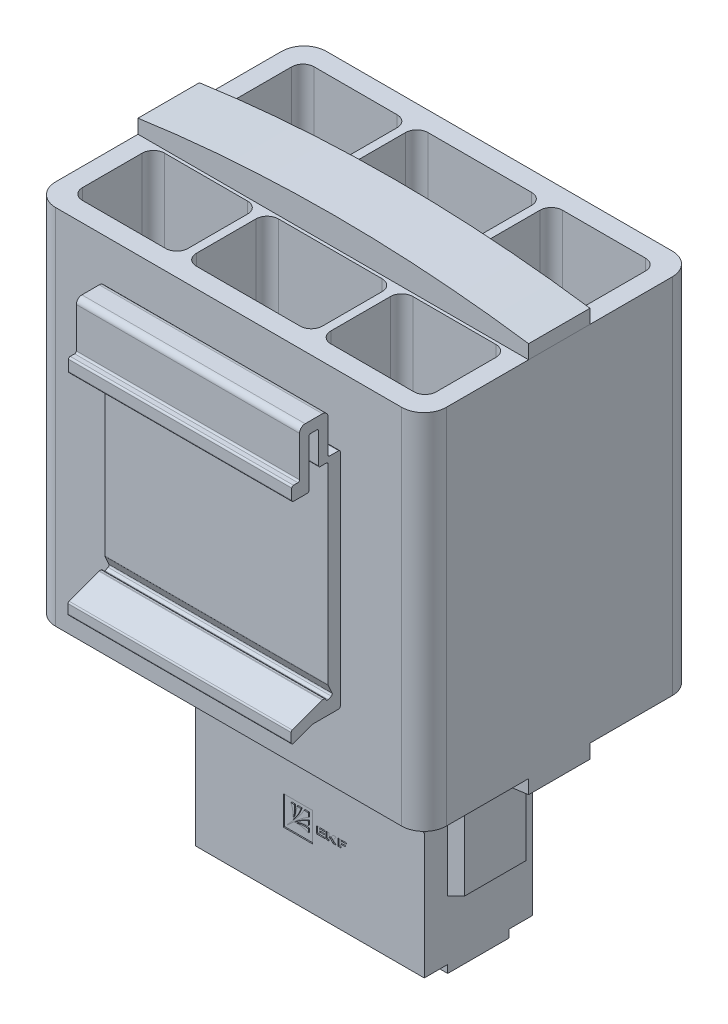
SolidWorks part; units mm, degrees
ref_plane "Спереди" through (0, 0, 0) normal (0, 0, 1) x (1, 0, 0)
ref_plane "Сверху" through (0, 0, 0) normal (0, 1, 0) x (1, 0, 0)
ref_plane "Справа" through (0, 0, 0) normal (1, 0, 0) x (0, 0, -1)
sketch "Эскиз1" plane through (0, 0, 0) normal (0, 0, 1) x (1, 0, 0)
  line L1 (-35, -32.5) -> (35, -32.5)
  line L2 (-35, -32.5) -> (-35, 32.5)
  line L3 (-35, 32.5) -> (35, 32.5)
  line L4 (35, -32.5) -> (35, 32.5)
  line L5 (-35, -32.5) -> (35, 32.5) construction
  line L6 (-35, 32.5) -> (35, -32.5) construction
  point P0 (0, 0)
  dimension "D1" = 70
  dimension "D2" = 65
extrude "Бобышка-Вытянуть1" add sketch "Эскиз1" along normal blind 48.5
sketch "Эскиз2" plane through (0, 32.5, 0) normal (0, 1, 0) x (1, 0, 0)
  line L0 (0, 0) -> (0, -10.85) construction
  line L1 (-11.3, -3.5) -> (11.3, -3.5)
  line L2 (-11.3, -3.5) -> (-11.3, -18.2)
  line L3 (-11.3, -18.2) -> (11.3, -18.2)
  line L4 (11.3, -3.5) -> (11.3, -18.2)
  line L5 (-11.3, -3.5) -> (11.3, -18.2) construction
  line L6 (-11.3, -18.2) -> (11.3, -3.5) construction
  line L7 (12.8, -3.5) -> (31.7, -3.5)
  line L8 (12.8, -3.5) -> (12.8, -18.2)
  line L9 (12.8, -18.2) -> (31.7, -18.2)
  line L10 (31.7, -3.5) -> (31.7, -18.2)
  line L11 (12.8, -3.5) -> (31.7, -18.2) construction
  line L12 (12.8, -18.2) -> (31.7, -3.5) construction
  line L13 (-31.7, -3.5) -> (-12.8, -3.5)
  line L14 (-31.7, -3.5) -> (-31.7, -18.2)
  line L15 (-31.7, -18.2) -> (-12.8, -18.2)
  line L16 (-12.8, -3.5) -> (-12.8, -18.2)
  line L17 (-31.7, -3.5) -> (-12.8, -18.2) construction
  line L18 (-31.7, -18.2) -> (-12.8, -3.5) construction
  line L19 (35, 0) -> (-35, 0) construction
  line L20 (-35, -24.25) -> (35, -24.25) construction
  line L21 (-35, -48.5) -> (-35, 0) construction
  line L22 (35, -48.5) -> (35, 0) construction
  line L23 (12.8, -30.3) -> (31.7, -30.3)
  line L24 (31.7, -45) -> (31.7, -30.3)
  line L25 (12.8, -45) -> (31.7, -45)
  line L26 (12.8, -45) -> (12.8, -30.3)
  line L27 (-11.3, -30.3) -> (11.3, -30.3)
  line L28 (11.3, -45) -> (11.3, -30.3)
  line L29 (-11.3, -45) -> (11.3, -45)
  line L30 (-11.3, -45) -> (-11.3, -30.3)
  line L31 (-31.7, -30.3) -> (-12.8, -30.3)
  line L32 (-12.8, -45) -> (-12.8, -30.3)
  line L33 (-31.7, -45) -> (-12.8, -45)
  line L34 (-31.7, -45) -> (-31.7, -30.3)
  point P0 (0, -10.85)
  point P5 (22.25, -10.85)
  point P10 (-22.25, -10.85)
  dimension "D1" = 22.6
  dimension "D2" = 18.9
  dimension "D3" = 1.5
  dimension "D4" = 1.5
  dimension "D5" = 3.5
  dimension "D6" = 14.7
extrude "Вырез-Вытянуть1" cut sketch "Эскиз2" against normal up to next
sketch "Эскиз3" plane through (0, 32.5, 0) normal (0, 1, 0) x (1, 0, 0)
  line L0 (35, -48.5) -> (35, 0) construction
  line L1 (-35, -29.75) -> (35, -29.75)
  line L2 (-35, -29.75) -> (-35, -18.75)
  line L3 (-35, -18.75) -> (35, -18.75)
  line L4 (35, -29.75) -> (35, -18.75)
  line L5 (-35, -29.75) -> (35, -18.75) construction
  line L6 (-35, -18.75) -> (35, -29.75) construction
  line L7 (0, 0) -> (0, -24.25) construction
  line L8 (35, 0) -> (-35, 0) construction
  line L9 (0, -24.25) -> (35, -24.25) construction
  point P0 (0, -24.25)
  point P11 (0, -24.4908)
  point P13 (35, -26.6567)
  point P14 (35, -27.6078)
  point P15 (35, -24.25)
  dimension "D1" = 11
extrude "Бобышка-Вытянуть2" add sketch "Эскиз3" along normal blind 5 separate body
sketch "Эскиз4" plane through (0, 0, 29.75) normal (0, 0, 1) x (1, 0, 0)
  line L0 (-35, 37.5) -> (-35, 32.5) construction
  line L1 (35, 37.5) -> (35, 32.5) construction
  line L2 (-35, 37.5) -> (35, 37.5) construction
  line L3 (-35, 32.5) -> (35, 32.5) construction
  line L4 (-35, 35) -> (-35, 41)
  line L5 (-35, 41) -> (35, 41)
  line L6 (35, 41) -> (35, 35)
  arc A0 (-35, 35) -> (35, 35) centre (0, -208.75) cw
  point P3 (0, 37.5)
  dimension "D1" = 2.5
  dimension "D2" = 6
extrude "Вырез-Вытянуть4" cut sketch "Эскиз4" against normal up to surface (11 mm away) up to face at (0, 35, 18.75)
ref_plane "Плоскость1" through (0, 0, 0) normal (0, 1, 0) x (1, 0, 0)
mirror "Зеркальное отражение2" about plane through (0, 0, 0) normal (0, 1, 0) of "Вырез-Вытянуть4", "Бобышка-Вытянуть2"
ref_plane "Плоскость2" through (0, 0, 24.25) normal (0, 0, -1) x (-1, 0, 0)
sketch "Эскиз5" plane through (0, 0, 24.25) normal (0, 0, -1) x (-1, 0, 0)
  line L0 (-23.5, -36.3761) -> (-23.5, -56.5)
  line L1 (-23.5, -56.5) -> (-20.5, -58)
  line L2 (-20.5, -58) -> (-20.5, -70)
  line L3 (-20.5, -70) -> (20.5, -70)
  line L4 (20.5, -70) -> (20.5, -58)
  line L5 (20.5, -58) -> (23.5, -56.5)
  line L6 (23.5, -56.5) -> (23.5, -36.3761)
  line L7 (0, -37.5) -> (0, -70) construction
  line L8 (-35, -32.5) -> (35, -32.5) construction
  arc A0 (-35, -35) -> (35, -35) centre (0, 208.75) ccw construction
  arc A1 (-23.5, -36.3761) -> (23.5, -36.3761) centre (0, 208.75) ccw
  point P7 (0, 0)
  point P16 (20.5, -52.5448)
  point P17 (15.9846, -51.6789)
  point P18 (20.5, -56.8538)
  point P19 (0, 0)
  point P20 (-23.5, -53.7094)
  point P21 (-20.5, -55.2234)
  point P22 (-23.5, -51.2637)
  dimension "D1" = 37.5
  dimension "D2" = 41
  dimension "D3" = 47
  dimension "D4" = 12
  dimension "D5" = 13.5
extrude "Бобышка-Вытянуть3" add sketch "Эскиз5" along normal up to surface and the other way up to surface up to face at (0, -34.375, 18.75) other way up to face at (0, -34.375, 29.75)
sketch "Эскиз6" plane through (0, 0, 29.75) normal (0, 0, 1) x (1, 0, 0)
  line L0 (-20.5, -68.6) -> (-20.5, -41.6)
  line L1 (-20.5, -58) -> (-20.5, -70) construction
  line L2 (-20.5, -68.6) -> (20.5, -68.6)
  line L3 (20.5, -70) -> (20.5, -58) construction
  line L4 (20.5, -68.6) -> (20.5, -41.6)
  line L5 (-20.5, -70) -> (20.5, -70) construction
  arc A0 (-20.5, -41.6) -> (20.5, -41.6) centre (0, -81.125) cw
  point P11 (0, -36.6)
  point P12 (0, 0)
  dimension "D1" = 1.4
  dimension "D2" = 32
  dimension "D3" = 5
extrude "Бобышка-Вытянуть4" add sketch "Эскиз6" along normal blind 4.2
chamfer "Фаска1" distance 4 angle 45 1 edges at (0, -36.6, 33.95)
mirror "Зеркальное отражение3" about plane through (0, 0, 24.25) normal (0, 0, -1) of "Фаска1", "Бобышка-Вытянуть4"
sketch "Эскиз7" plane through (0, 0, 14.55) normal (0, 0, -1) x (-1, 0, 0)
  line L0 (0, -61.65) -> (0, -68.6) construction
  line L1 (-5.65, -57.4) -> (5.65, -57.4)
  line L2 (-5.65, -57.4) -> (-5.65, -65.9)
  line L3 (-5.65, -65.9) -> (5.65, -65.9)
  line L4 (5.65, -57.4) -> (5.65, -65.9)
  line L5 (-5.65, -57.4) -> (5.65, -65.9) construction
  line L6 (-5.65, -65.9) -> (5.65, -57.4) construction
  line L7 (-18.15, -57.4) -> (-6.85, -57.4)
  line L8 (-18.15, -57.4) -> (-18.15, -65.9)
  line L9 (-18.15, -65.9) -> (-6.85, -65.9)
  line L10 (-6.85, -57.4) -> (-6.85, -65.9)
  line L11 (-18.15, -57.4) -> (-6.85, -65.9) construction
  line L12 (-18.15, -65.9) -> (-6.85, -57.4) construction
  line L13 (6.85, -57.4) -> (18.15, -57.4)
  line L14 (6.85, -57.4) -> (6.85, -65.9)
  line L15 (6.85, -65.9) -> (18.15, -65.9)
  line L16 (18.15, -57.4) -> (18.15, -65.9)
  line L17 (6.85, -57.4) -> (18.15, -65.9) construction
  line L18 (6.85, -65.9) -> (18.15, -57.4) construction
  line L19 (20.5, -68.6) -> (-20.5, -68.6) construction
  line L20 (20.5, -68.6) -> (-20.5, -68.6) construction
  point P0 (0, -61.65)
  point P5 (-12.5, -61.65)
  point P10 (12.5, -61.65)
  dimension "D1" = 11.3
  dimension "D2" = 1.2
  dimension "D3" = 1.2
  dimension "D4" = 2.7
  dimension "D5" = 8.5
extrude "Бобышка-Вытянуть5" add sketch "Эскиз7" along normal blind 2 draft 12
sketch "Эскиз9" plane through (0, -70, 0) normal (0, -1, 0) x (1, 0, 0)
  line L0 (0, 27.25) -> (0, 0) construction
  line L1 (-14.5, 29.75) -> (-10.5, 29.75)
  line L2 (-14.5, 29.75) -> (-14.5, 24.75)
  line L3 (-14.5, 24.75) -> (-10.5, 24.75)
  line L4 (-10.5, 29.75) -> (-10.5, 24.75)
  line L5 (-14.5, 29.75) -> (-10.5, 24.75) construction
  line L6 (-14.5, 24.75) -> (-10.5, 29.75) construction
  line L7 (-2, 29.75) -> (2, 29.75)
  line L8 (-2, 29.75) -> (-2, 24.75)
  line L9 (-2, 24.75) -> (2, 24.75)
  line L10 (2, 29.75) -> (2, 24.75)
  line L11 (-2, 29.75) -> (2, 24.75) construction
  line L12 (-2, 24.75) -> (2, 29.75) construction
  line L13 (10.5, 29.75) -> (14.5, 29.75)
  line L14 (10.5, 29.75) -> (10.5, 24.75)
  line L15 (10.5, 24.75) -> (14.5, 24.75)
  line L16 (14.5, 29.75) -> (14.5, 24.75)
  line L17 (10.5, 29.75) -> (14.5, 24.75) construction
  line L18 (10.5, 24.75) -> (14.5, 29.75) construction
  line L19 (-12.5, 27.25) -> (0, 27.25) construction
  line L20 (0, 27.25) -> (12.5, 27.25) construction
  line L21 (-12.5, 12.55) -> (-12.5, 27.25) construction
  line L22 (-7.2751, 12.55) -> (-17.7249, 12.55) construction
  line L23 (12.5, 27.25) -> (12.5, 12.55) construction
  line L24 (17.7249, 12.55) -> (7.2751, 12.55) construction
  line L27 (-20.5, 29.75) -> (20.5, 29.75) construction
  point P0 (-12.5, 27.25)
  point P5 (0, 27.25)
  point P10 (12.5, 27.25)
  dimension "D1" = 4
  dimension "D2" = 5
extrude "Вырез-Вытянуть5" cut sketch "Эскиз9" against normal blind 7
sketch "Эскиз10" plane through (0, -70, 0) normal (0, -1, 0) x (1, 0, 0)
  line L0 (-20.5, 18.75) -> (20.5, 18.75) construction
  line L1 (-14.5, 24.75) -> (-10.5, 24.75)
  line L2 (-14.5, 24.75) -> (-14.5, 18.75)
  line L3 (-14.5, 18.75) -> (-10.5, 18.75)
  line L4 (-10.5, 24.75) -> (-10.5, 18.75)
  line L5 (-20.5, 18.75) -> (20.5, 18.75) construction
  line L6 (-2, 24.75) -> (2, 24.75)
  line L7 (-2, 24.75) -> (-2, 18.75)
  line L8 (-2, 18.75) -> (2, 18.75)
  line L9 (2, 24.75) -> (2, 18.75)
  line L10 (10.5, 24.75) -> (14.5, 24.75)
  line L11 (10.5, 24.75) -> (10.5, 18.75)
  line L12 (10.5, 18.75) -> (14.5, 18.75)
  line L13 (14.5, 24.75) -> (14.5, 18.75)
  line L14 (14.5, 24.75) -> (14.5, 29.75) construction
  line L15 (2, 24.75) -> (2, 29.75) construction
  line L16 (-10.5, 24.75) -> (-10.5, 29.75) construction
extrude "Вырез-Вытянуть6" cut sketch "Эскиз10" against normal up to surface (1.4 mm away) up to face at (0, -68.6, 16.65)
ref_plane "Плоскость3" through (0, 0, 0) normal (-1, 0, 0) x (0, 0, 1)
sketch "Эскиз11" plane through (0, 0, 0) normal (-1, 0, 0) x (0, 0, 1)
  line L0 (48.8, -19.7) -> (53.4465, -19.7)
  line L1 (53.5502, -19.7185) -> (56.8963, -20.9513)
  line L2 (57.3, -20.6698) -> (57.3, -19.0712)
  line L3 (57.1037, -18.7897) -> (51.7533, -16.8185)
  line L4 (51.6496, -16.8) -> (51.3956, -16.8)
  line L5 (51.1229, -16.975) -> (51.0531, -17.1273)
  line L6 (50.6554, -17.275) -> (50.1099, -17.025)
  line L7 (49.9622, -16.6273) -> (50.6727, -15.0772)
  line L8 (50.7, -14.9522) -> (50.7, 19.3)
  line L9 (51, 19.6) -> (52.1, 19.6)
  line L10 (52.4, 19.9) -> (52.4, 25.3)
  line L11 (52.7, 25.6) -> (53.8, 25.6)
  line L12 (54.1, 25.3) -> (54.1, 16.9)
  line L13 (54.4, 16.6) -> (56.9, 16.6)
  line L14 (57.2, 16.9) -> (57.2, 18.8)
  line L15 (56.9, 19.1) -> (56.1, 19.1)
  line L16 (55.8, 19.4) -> (55.8, 26.6)
  line L17 (54.8, 27.6) -> (51.7, 27.6)
  line L18 (50.7, 26.6) -> (50.7, 20.7)
  line L19 (50.4, 20.4) -> (48.8, 20.4)
  line L20 (48.5, 20.1) -> (48.5, -19.4)
  line L21 (48.5, 32.5) -> (48.5, -32.5) construction
  line L22 (48.5, 32.5) -> (0, 32.5) construction
  arc A0 (48.8, -19.7) -> (48.5, -19.4) centre (48.8, -19.4) cw
  arc A1 (53.4465, -19.7) -> (53.5502, -19.7185) centre (53.4465, -20) cw
  arc A2 (57.3, -19.0712) -> (57.1037, -18.7897) centre (57, -19.0712) ccw
  arc A3 (56.8963, -20.9513) -> (57.3, -20.6698) centre (57, -20.6698) ccw
  arc A4 (51.7533, -16.8185) -> (51.6496, -16.8) centre (51.6496, -17.1) ccw
  arc A5 (51.3956, -16.8) -> (51.1229, -16.975) centre (51.3956, -17.1) ccw
  arc A6 (50.6727, -15.0772) -> (50.7, -14.9522) centre (50.4, -14.9522) ccw
  arc A7 (50.1099, -17.025) -> (49.9622, -16.6273) centre (50.2349, -16.7523) cw
  arc A8 (51.0531, -17.1273) -> (50.6554, -17.275) centre (50.7804, -17.0023) cw
  arc A9 (54.1, 16.9) -> (54.4, 16.6) centre (54.4, 16.9) ccw
  arc A10 (56.9, 16.6) -> (57.2, 16.9) centre (56.9, 16.9) ccw
  arc A11 (57.2, 18.8) -> (56.9, 19.1) centre (56.9, 18.8) ccw
  arc A12 (56.1, 19.1) -> (55.8, 19.4) centre (56.1, 19.4) cw
  arc A13 (48.8, 20.4) -> (48.5, 20.1) centre (48.8, 20.1) ccw
  arc A14 (50.7, 20.7) -> (50.4, 20.4) centre (50.4, 20.7) cw
  arc A15 (50.7, 19.3) -> (51, 19.6) centre (51, 19.3) cw
  arc A16 (52.1, 19.6) -> (52.4, 19.9) centre (52.1, 19.9) ccw
  arc A17 (52.4, 25.3) -> (52.7, 25.6) centre (52.7, 25.3) cw
  arc A18 (53.8, 25.6) -> (54.1, 25.3) centre (53.8, 25.3) cw
  arc A19 (51.7, 27.6) -> (50.7, 26.6) centre (51.7, 26.6) ccw
  arc A20 (55.8, 26.6) -> (54.8, 27.6) centre (54.8, 26.6) ccw
  point P21 (53.25, 25.6)
  point P22 (53.25, 27.6)
  point P65 (48.5, 20.1)
  dimension "D7" = 0.3
  dimension "D8" = 1
  dimension "D1" = 2.1
  dimension "D2" = 2.2
  dimension "D3" = 47.3
  dimension "D4" = 6.5
  dimension "D5" = 2
  dimension "D6" = 11
  dimension "D9" = 7.2
  dimension "D10" = 12.4
extrude "Бобышка-Вытянуть6" add sketch "Эскиз11" along normal mid plane 40
fillet "Скругление1" radius 4 4 edges at (35, 0, 0) (35, 0, 48.5) (-35, 0, 0) (-35, 0, 48.5)
fillet "Скругление2" radius 2 24 edges at (-12.8, 0, 3.5) (-12.8, 0, 18.2) (-31.7, 0, 18.2) (-31.7, 0, 3.5) (-11.3, 0, 3.5) (-11.3, 0, 18.2) (11.3, 0, 18.2) (11.3, 0, 3.5) (31.7, 0, 18.2) (12.8, 0, 18.2) (12.8, 0, 3.5) (31.7, 0, 3.5) (31.7, 0, 30.3) (12.8, 0, 30.3) (12.8, 0, 45) (31.7, 0, 45) (11.3, 0, 45) (11.3, 0, 30.3) (-11.3, 0, 30.3) (-11.3, 0, 45) (-12.8, 0, 45) (-12.8, 0, 30.3) (-31.7, 0, 30.3) (-31.7, 0, 45)
sketch "Эскиз12" plane through (0, 0, 33.95) normal (0, 0, 1) x (1, 0, 0)
  line L0 (-4.7623, -57.8049) -> (0.4559, -57.8049)
  line L1 (0.4559, -57.8049) -> (0.4559, -52.5968)
  line L2 (0.4559, -52.5968) -> (-4.7623, -52.5968)
  line L3 (-4.7623, -52.5968) -> (-4.7623, -57.8049)
  line L4 (-0.2878, -56.4724) -> (-0.2878, -55.8157)
  line L5 (-0.2878, -55.3576) -> (-0.2878, -54.6088)
  line L6 (-0.2878, -54.0846) -> (-0.2878, -53.3358)
  line L7 (-0.2878, -53.3358) -> (-1.0366, -53.3358)
  line L8 (-1.5608, -53.3358) -> (-2.3096, -53.3358)
  line L9 (-2.7678, -53.3358) -> (-3.4245, -53.3358)
  line L10 (4.9957, -54.6088) -> (4.9957, -55.8788)
  line L11 (4.9957, -55.8788) -> (5.5487, -55.8788)
  line L12 (5.5487, -55.8788) -> (5.5487, -55.3028)
  line L13 (5.5487, -55.3028) -> (6.4242, -55.3028)
  line L14 (6.4242, -55.3028) -> (6.4242, -55.1185)
  line L15 (6.4242, -55.1185) -> (5.5487, -55.1185)
  line L16 (5.5487, -55.1185) -> (5.5487, -54.8017)
  line L17 (5.5487, -54.8017) -> (6.5221, -54.8017)
  line L18 (6.5221, -54.8017) -> (6.5221, -54.6088)
  line L19 (6.5221, -54.6088) -> (4.9957, -54.6088)
  line L20 (3.4256, -55.3146) -> (3.5753, -55.3146)
  line L21 (3.7486, -55.3966) -> (4.1255, -55.879)
  line L22 (4.1255, -55.879) -> (4.7015, -55.879)
  line L23 (4.7015, -55.879) -> (4.2295, -55.2749)
  line L24 (4.2295, -55.2395) -> (4.7192, -54.6127)
  line L25 (4.7192, -54.6127) -> (4.138, -54.6127)
  line L26 (4.138, -54.6127) -> (3.8365, -54.9985)
  line L27 (3.6848, -55.1099) -> (3.4256, -55.1099)
  line L28 (3.4256, -55.1099) -> (3.4256, -54.6088)
  line L29 (3.4256, -54.6088) -> (2.8714, -54.6088)
  line L30 (2.8714, -54.6088) -> (2.8714, -55.5389)
  line L31 (2.9978, -55.879) -> (3.4256, -55.879)
  line L32 (3.4256, -55.879) -> (3.4256, -55.3146)
  line L33 (1.713, -55.3115) -> (2.6058, -55.3115)
  line L34 (2.6058, -55.3115) -> (2.6058, -55.1099)
  line L35 (2.6058, -55.1099) -> (1.713, -55.1099)
  line L36 (1.713, -55.1099) -> (1.713, -54.8104)
  line L37 (1.713, -54.8104) -> (2.6922, -54.8104)
  line L38 (2.6922, -54.8104) -> (2.6922, -54.6088)
  line L39 (2.6922, -54.6088) -> (1.1658, -54.6088)
  line L40 (1.1658, -54.6088) -> (1.1658, -55.5389)
  line L41 (1.3167, -55.879) -> (2.6922, -55.879)
  line L42 (2.6922, -55.879) -> (2.6922, -55.6859)
  line L43 (2.6922, -55.6859) -> (1.713, -55.6859)
  line L44 (1.713, -55.6859) -> (1.713, -55.3115)
  arc A0 (-2.2891, -55.9741) -> (-2.3108, -56.0028) centre (-2.282, -56.002) ccw
  arc A1 (-2.3101, -56.0114) -> (-2.28, -56.0366) centre (-2.2815, -56.0078) ccw
  arc A2 (-2.7273, -56.0263) -> (-2.7365, -56.0411) centre (-2.7086, -56.0482) ccw
  arc A3 (-2.7051, -56.0853) -> (-2.6905, -56.0813) centre (-2.7052, -56.0565) ccw
  arc A4 (-4.0035, -56.9961) -> (-3.941, -57.0444) centre (-3.9723, -57.0203) ccw
  arc A5 (-3.0334, -55.7384) -> (-3.0374, -55.7531) centre (-3.0086, -55.7531) ccw
  arc A6 (-2.9932, -55.7844) -> (-2.9783, -55.7752) centre (-3.0003, -55.7565) ccw
  arc A7 (-2.9886, -55.3279) -> (-2.9635, -55.358) centre (-2.9599, -55.3294) ccw
  arc A8 (-2.9549, -55.3587) -> (-2.9262, -55.337) centre (-2.9541, -55.3299) ccw
  arc A9 (4.2295, -55.2395) -> (4.2295, -55.2749) centre (4.2522, -55.2572) ccw
  arc A10 (1.1658, -55.5389) -> (1.2031, -55.7428) centre (1.7418, -55.5389) ccw
  arc A11 (1.275, -55.8611) -> (1.3167, -55.879) centre (1.3167, -55.8214) ccw
  spline S0 degree 3 poles (-2.3108, -56.0028) (-2.3107, -56.0055) (-2.3104, -56.0083) (-2.3101, -56.0112) (-2.3101, -56.0114) knots 0 0 0 0 0.917925 1 1 1 1 weights 1 1 1 1 1
  spline S1 degree 3 poles (-2.28, -56.0366) (-2.1578, -56.0302) (-1.9642, -56.0247) (-1.7062, -56.0429) (-1.5152, -56.0764) (-1.3316, -56.1033) (-1.1555, -56.1447) (-0.9802, -56.1841) (-0.8245, -56.2398) (-0.6821, -56.2886) (-0.5586, -56.3424) (-0.428, -56.4027) (-0.3378, -56.4431) (-0.2878, -56.4724) knots 0 0 0 0 0.17778 0.281267 0.375033 0.459576 0.550813 0.637751 0.720424 0.790855 0.856523 0.915971 1 1 1 1 weights 1 1 1 1 1 1 1 1 1 1 1 1 1 1
  spline S2 degree 3 poles (-0.2878, -55.8157) (-0.3641, -55.8032) (-0.4985, -55.7967) (-0.6992, -55.7882) (-0.8823, -55.7781) (-1.0785, -55.7775) (-1.278, -55.7903) (-1.4931, -55.8038) (-1.7021, -55.8301) (-1.895, -55.867) (-2.0896, -55.9069) (-2.2145, -55.9553) (-2.2891, -55.9741) knots 0 0 0 0 0.114393 0.199277 0.298132 0.386384 0.490042 0.594519 0.706019 0.802157 0.885931 1 1 1 1 weights 1 1 1 1 1 1 1 1 1 1 1 1 1
  spline S3 degree 3 poles (-0.2878, -54.6088) (-0.5329, -54.6925) (-0.8841, -54.8599) (-1.3505, -55.0916) (-1.6718, -55.2895) (-1.9725, -55.4796) (-2.2214, -55.6507) (-2.4266, -55.7958) (-2.5821, -55.921) (-2.6834, -55.9889) (-2.7273, -56.0263) knots 0 0 0 0 0.273618 0.411874 0.551161 0.673016 0.788626 0.871078 0.939011 1 1 1 1 weights 1 1 1 1 1 1 1 1 1 1 1
  spline S4 degree 3 poles (-2.7365, -56.0411) (-2.7393, -56.052) (-2.741, -56.0785) (-2.7159, -56.0853) (-2.7051, -56.0853) knots 0 0 0 0 0.510001 1 1 1 1 weights 1 1 1 1 1
  spline S5 degree 3 poles (-2.6905, -56.0813) (-2.5839, -56.0182) (-2.4049, -55.9256) (-2.151, -55.8002) (-1.9301, -55.7027) (-1.6944, -55.6186) (-1.4515, -55.5398) (-1.1994, -55.4816) (-0.9577, -55.435) (-0.7392, -55.3998) (-0.5191, -55.3773) (-0.3726, -55.3658) (-0.2878, -55.3576) knots 0 0 0 0 0.146583 0.238456 0.335283 0.432158 0.534641 0.637315 0.738125 0.826097 0.899195 1 1 1 1 weights 1 1 1 1 1 1 1 1 1 1 1 1 1
  spline S6 degree 3 poles (-1.0366, -53.3358) (-1.083, -53.4462) (-1.1753, -53.6131) (-1.3197, -53.8436) (-1.4521, -54.0363) (-1.5929, -54.2388) (-1.7418, -54.4405) (-1.8988, -54.6537) (-2.0732, -54.8663) (-2.2483, -55.0792) (-2.4156, -55.2772) (-2.5682, -55.459) (-2.7237, -55.6261) (-2.914, -55.8304) (-3.3437, -56.2867) (-3.7103, -56.6959) (-4.0035, -56.9961) knots 0 0 0 0 0.075851 0.120866 0.172576 0.224175 0.277338 0.331656 0.392142 0.451757 0.506605 0.556596 0.602323 0.651423 0.733779 1 1 1 1 weights 1 1 1 1 1 1 1 1 1 1 1 1 1 1 1 1 1
  spline S7 degree 3 poles (-3.941, -57.0444) (-3.6429, -56.7537) (-3.2363, -56.3893) (-2.7825, -55.9619) (-2.5781, -55.7716) (-2.411, -55.6161) (-2.2293, -55.4635) (-2.0313, -55.2962) (-1.8184, -55.1211) (-1.6058, -54.9468) (-1.3926, -54.7897) (-1.1909, -54.6408) (-0.9884, -54.5) (-0.7957, -54.3676) (-0.5652, -54.2233) (-0.3983, -54.1309) (-0.2878, -54.0846) knots 0 0 0 0 0.264644 0.347178 0.396382 0.442208 0.492307 0.547272 0.607015 0.667632 0.722066 0.775343 0.827053 0.878874 0.923986 1 1 1 1 weights 1 1 1 1 1 1 1 1 1 1 1 1 1 1 1 1 1
  spline S8 degree 3 poles (-3.0374, -55.7531) (-3.0374, -55.7638) (-3.0306, -55.7889) (-3.004, -55.7872) (-2.9932, -55.7844) knots 0 0 0 0 0.489999 1 1 1 1 weights 1 1 1 1 1
  spline S9 degree 3 poles (-2.9783, -55.7752) (-2.941, -55.7313) (-2.8731, -55.63) (-2.7479, -55.4745) (-2.6028, -55.2693) (-2.4317, -55.0204) (-2.2416, -54.7197) (-2.0437, -54.3984) (-1.812, -53.932) (-1.6446, -53.5808) (-1.5608, -53.3358) knots 0 0 0 0 0.060989 0.128922 0.211374 0.326984 0.448839 0.588126 0.726382 1 1 1 1 weights 1 1 1 1 1 1 1 1 1 1 1
  spline S10 degree 3 poles (-2.3096, -53.3358) (-2.3179, -53.4205) (-2.3294, -53.567) (-2.3518, -53.7871) (-2.3871, -54.0056) (-2.4337, -54.2474) (-2.4919, -54.4994) (-2.5707, -54.7423) (-2.6548, -54.978) (-2.7523, -55.1989) (-2.8777, -55.4528) (-2.9703, -55.6318) (-3.0334, -55.7384) knots 0 0 0 0 0.100805 0.173903 0.261875 0.362685 0.465359 0.567842 0.664717 0.761544 0.853417 1 1 1 1 weights 1 1 1 1 1 1 1 1 1 1 1 1 1
  spline S11 degree 3 poles (-3.4245, -53.3358) (-3.3952, -53.3857) (-3.3548, -53.4759) (-3.2945, -53.6065) (-3.2407, -53.73) (-3.1919, -53.8724) (-3.1362, -54.0281) (-3.0968, -54.2035) (-3.0554, -54.3795) (-3.0285, -54.5631) (-2.995, -54.7541) (-2.9768, -55.0121) (-2.9823, -55.2057) (-2.9886, -55.3279) knots 0 0 0 0 0.084029 0.143477 0.209145 0.279576 0.362249 0.449187 0.540424 0.624967 0.718733 0.82222 1 1 1 1 weights 1 1 1 1 1 1 1 1 1 1 1 1 1 1
  spline S12 degree 3 poles (-2.9635, -55.358) (-2.9633, -55.358) (-2.9604, -55.3584) (-2.9575, -55.3587) (-2.9549, -55.3587) knots 0 0 0 0 0.082075 1 1 1 1 weights 1 1 1 1 1
  spline S13 degree 3 poles (-2.9262, -55.337) (-2.9073, -55.2624) (-2.8589, -55.1375) (-2.8191, -54.9429) (-2.7822, -54.75) (-2.7559, -54.541) (-2.7424, -54.3259) (-2.7296, -54.1264) (-2.7302, -53.9303) (-2.7403, -53.7471) (-2.7488, -53.5464) (-2.7553, -53.412) (-2.7678, -53.3358) knots 0 0 0 0 0.114069 0.197843 0.293981 0.405481 0.509958 0.613616 0.701868 0.800723 0.885607 1 1 1 1 weights 1 1 1 1 1 1 1 1 1 1 1 1 1
  spline S14 degree 3 poles (3.5753, -55.3146) (3.6105, -55.3171) (3.6771, -55.3303) (3.7305, -55.372) (3.7486, -55.3966) knots 0 0 0 0 0.539816 1 1 1 1 weights 1 1 1 1 1
  spline S15 degree 3 poles (3.8365, -54.9985) (3.8087, -55.0355) (3.7843, -55.0537) (3.7212, -55.1005) (3.6848, -55.1099) knots 0 0 0 0 0.375989 1 1 1 1 weights 1 1 1 1 1
  spline S16 degree 3 poles (2.8714, -55.5389) (2.8729, -55.5791) (2.884, -55.6372) (2.9033, -55.7123) (2.9252, -55.7602) (2.9533, -55.8175) (2.9797, -55.855) (2.9978, -55.879) knots 0 0 0 0 0.326178 0.481344 0.628375 0.754487 1 1 1 1 weights 1 1 1 1 1 1 1 1
  spline S17 degree 3 poles (1.2031, -55.7428) (1.2053, -55.7488) (1.217, -55.7775) (1.2397, -55.8183) (1.2644, -55.85) (1.275, -55.8611) knots 0 0 0 0 0.137108 0.669562 1 1 1 1 weights 1 1 1 1 1 1
extrude "Вырез-Вытянуть7" cut sketch "Эскиз12" against normal blind 0.2
